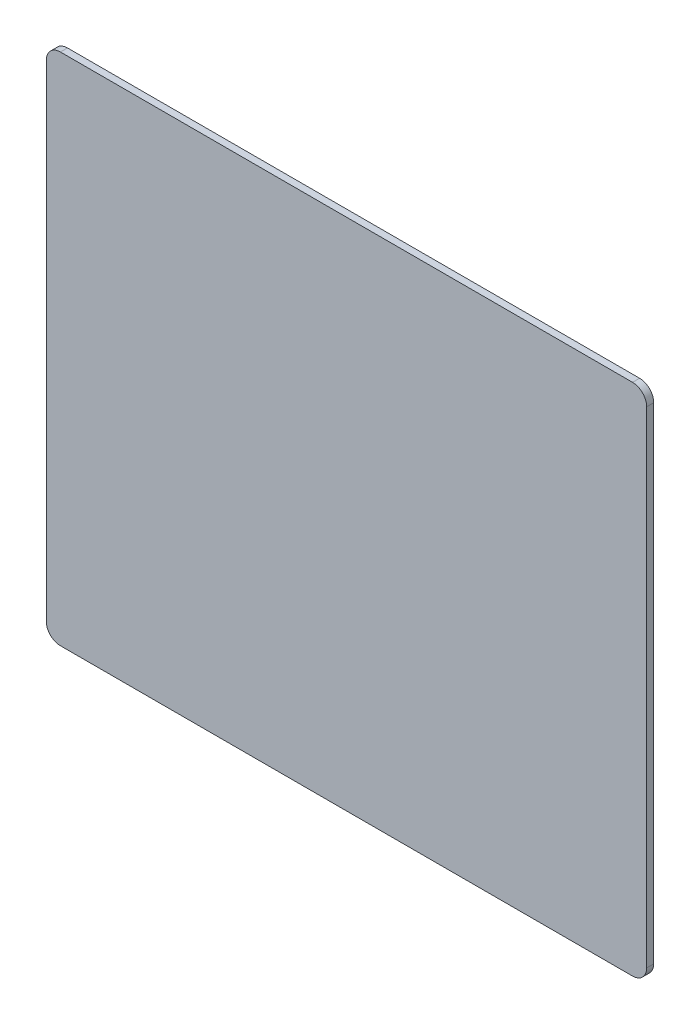
SolidWorks part; units mm, degrees
ref_plane "Plan de face" through (0, 0, 0) normal (0, 0, 1) x (1, 0, 0)
ref_plane "Plan de dessus" through (0, 0, 0) normal (0, 1, 0) x (1, 0, 0)
ref_plane "Plan de droite" through (0, 0, 0) normal (1, 0, 0) x (0, 0, -1)
sketch "Esquisse1" plane through (0, 0, 0) normal (0, 0, 1) x (1, 0, 0)
  line L1 (-40.5, 36.4) -> (40.5, 36.4)
  line L2 (-42.5, 34.4) -> (-42.5, -34.4)
  line L3 (-40.5, -36.4) -> (40.5, -36.4)
  line L4 (42.5, 34.4) -> (42.5, -34.4)
  line L5 (-42.5, 36.4) -> (42.5, -36.4) construction
  line L6 (-42.5, -36.4) -> (42.5, 36.4) construction
  arc A0 (-42.5, -34.4) -> (-40.5, -36.4) centre (-40.5, -34.4) ccw
  arc A1 (40.5, -36.4) -> (42.5, -34.4) centre (40.5, -34.4) ccw
  arc A2 (40.5, 36.4) -> (42.5, 34.4) centre (40.5, 34.4) cw
  arc A3 (-40.5, 36.4) -> (-42.5, 34.4) centre (-40.5, 34.4) ccw
  point P0 (0, 0)
  dimension "D3" = 2
  dimension "D1" = 85
  dimension "D2" = 72.8
extrude "Boss.-Extru.1" add sketch "Esquisse1" along normal blind 1
sketch "Esquisse2" plane through (0, 0, 0) normal (0, 0, -1) x (-1, 0, 0)
  line L0 (-35.5, 28.4) -> (-35.5, 19.4)
  line L1 (-35.5, 19.4) -> (-31.627, 18.4)
  line L2 (-31.627, 18.4) -> (-20.5, 18.4)
  line L3 (-20.5, 18.4) -> (-20.5, 28.4)
  line L4 (-20.5, 28.4) -> (-35.5, 28.4)
  line L5 (-42.5, -34.4) -> (-42.5, 34.4) construction
  line L6 (-40.5, 36.4) -> (40.5, 36.4) construction
  dimension "D1" = 15
  dimension "D2" = 10
  dimension "D3" = 9
  dimension "D4" = 4
  dimension "D5" = 7
  dimension "D6" = 8
extrude "Boss.-Extru.2" add sketch "Esquisse2" along normal blind 0.2
pattern_linear "Répétition linéaire1" count 4 spacing 19 along (-1, 0, 0) count 5 spacing 12 along (0, -1, 0) skipping (3, 3), (3, 4) of "Boss.-Extru.2"
sketch "Esquisse3" plane through (0, 0, 0) normal (0, 0, -1) x (-1, 0, 0)
  line L1 (21.5, -7.6) -> (36.5, -7.6) construction
  line L2 (36.5, -7.6) -> (36.5, -17.6) construction
  line L3 (36.5, -17.6) -> (21.5, -17.6) construction
  line L4 (21.5, -17.6) -> (21.5, -7.6) construction
  line L5 (36.5, -5.6) -> (36.5, 4.4) construction
  line L6 (21.5, 4.4) -> (21.5, -4.6) construction
  line L7 (6.373, -17.6) -> (17.5, -17.6) construction
  line L8 (17.5, -7.6) -> (2.5, -7.6) construction
  ellipse E0 centre (29, -12.6) end of major axis (36.5, -12.6) minor radius 5
extrude "Boss.-Extru.3" add sketch "Esquisse3" along normal blind 0.2
pattern_linear "Répétition linéaire2" count 2 spacing 12 along (0, -1, 0) of "Boss.-Extru.3"
sketch "Esquisse4" plane through (0, 0, -0.2) normal (0, 0, -1) x (-1, 0, 0)
  line L0 (-20.5, 18.4) -> (-20.5, 28.4) construction
  line L1 (-31.75, 20.4) -> (-20.5, 20.4) construction
  line L2 (-31.75, 20.4) -> (-31.75, 33.0905) construction
  line L4 (-20.5, 28.4) -> (-35.5, 28.4) construction
  line L5 (-12.75, 20.4) -> (-3.304, 20.4) construction
  line L6 (-1.5, 28.4) -> (-16.5, 28.4) construction
  line L7 (7, 20.4) -> (15.4189, 20.4) construction
  line L8 (27, 18.9) -> (33.7413, 18.9) construction
  line L9 (-30, 8.4) -> (-22.7278, 8.4) construction
  line L10 (-30, -3.6) -> (-22.7278, -3.6) construction
  line L11 (-11, 8.4) -> (-3.304, 8.4) construction
  line L12 (8, 8.4) -> (15.4189, 8.4) construction
  line L13 (24.3298, 8.4) -> (33.7413, 8.4) construction
  line L14 (24.3298, -3.6) -> (33.7413, -3.6) construction
  line L15 (8, -3.6) -> (14.3175, -3.6) construction
  line L16 (-11, -3.6) -> (-4.8059, -3.6) construction
  line L17 (-30, -15.6) -> (-22.7278, -15.6) construction
  line L18 (-11, -15.6) -> (-3.304, -15.6) construction
  line L19 (8, -15.6) -> (14.3175, -15.6) construction
  line L20 (-31.75, -27.6) -> (-23.9293, -27.6) construction
  line L21 (23.5, -15.6) -> (35.7582, -15.6) construction
  line L22 (-11, -27.6) -> (-4.8059, -27.6) construction
  line L23 (6, -27.6) -> (14.3175, -27.6) construction
  line L24 (23.5, -26.6827) -> (31.8102, -26.6827) construction
  line L25 (17.5, 28.4) -> (2.5, 28.4) construction
  line L26 (36.5, 28.4) -> (21.5, 28.4) construction
  line L27 (36.5, 28.4) -> (21.5, 28.4) construction
  line L28 (-20.5, 16.4) -> (-35.5, 16.4) construction
  line L29 (-20.5, 4.4) -> (-35.5, 4.4) construction
  line L30 (-20.5, -7.6) -> (-35.5, -7.6) construction
  line L31 (-20.5, -19.6) -> (-35.5, -19.6) construction
  line L32 (-1.5, 16.4) -> (-16.5, 16.4) construction
  line L33 (17.5, 16.4) -> (2.5, 16.4) construction
  line L34 (28, 8.4) -> (28, 12.4)
  line L35 (28, 12.4) -> (26.5, 12.4)
  line L36 (26.5, 12.4) -> (29, 15.4)
  line L37 (29, 15.4) -> (31.5, 12.4)
  line L38 (31.5, 12.4) -> (30, 12.4)
  line L39 (30, 12.4) -> (30, 8.4)
  line L40 (30, 8.4) -> (28, 8.4)
  line L41 (36.5, 16.4) -> (21.5, 16.4) construction
  line L44 (28, 3.4) -> (28, -0.6)
  line L52 (28, -0.6) -> (26.5, -0.6)
  line L53 (26.5, -0.6) -> (29, -3.6)
  line L54 (29, -3.6) -> (31.5, -0.6)
  line L55 (31.5, -0.6) -> (30, -0.6)
  line L56 (30, -0.6) -> (30, 3.4)
  line L57 (30, 3.4) -> (28, 3.4)
  line L58 (-24, -23.6) -> (-24, -25.6)
  line L59 (-24, -25.6) -> (-28, -25.6)
  line L60 (-28, -25.6) -> (-28, -27.1)
  line L61 (-28, -27.1) -> (-31, -24.6)
  line L62 (-31, -24.6) -> (-28, -22.1)
  line L63 (-28, -22.1) -> (-28, -23.6)
  line L64 (-28, -23.6) -> (-24, -23.6)
  line L65 (6, -23.6) -> (6, -25.6)
  line L66 (6, -25.6) -> (10, -25.6)
  line L67 (10, -25.6) -> (10, -27.1)
  line L68 (10, -27.1) -> (13, -24.6)
  line L69 (13, -24.6) -> (10, -22.1)
  line L70 (10, -22.1) -> (10, -23.6)
  line L71 (10, -23.6) -> (6, -23.6)
  line L72 (-20.5, -19.6) -> (-35.5, -19.6) construction
  line L73 (-20.5, -29.6) -> (-20.5, -19.6) construction
  line L74 (17.5, -19.6) -> (2.5, -19.6) construction
  line L75 (36.5, 4.4) -> (21.5, 4.4) construction
  text T0 "F1" font "Century Gothic" height in points 22
  text T1 "F2" font "Century Gothic" height in points 22
  text T2 "#" font "Century Gothic" height in points 22
  text T3 "*" font "Century Gothic" height in points 22
  text T4 "1" font "Century Gothic" height in points 22
  text T5 "2" font "Century Gothic" height in points 22
  text T6 "3" font "Century Gothic" height in points 22
  text T7 "4" font "Century Gothic" height in points 22
  text T8 "5" font "Century Gothic" height in points 22
  text T9 "6" font "Century Gothic" height in points 22
  text T10 "7" font "Century Gothic" height in points 22
  text T11 "8" font "Century Gothic" height in points 22
  text T12 "9" font "Century Gothic" height in points 22
  text T13 "0" font "Century Gothic" height in points 22
  text T14 "Esc" font "Century Gothic" height in points 20
  text T15 "Ent" font "Century Gothic" height in points 20
  point P10 (-28, 28.4)
  point P14 (-9, 28.4)
  point P54 (10, 28.4)
  point P58 (29, 28.4)
  point P72 (-28, 16.4)
  point P75 (-9, 16.4)
  point P78 (10, 16.4)
  point P87 (29, 16.4)
  point P113 (-28, -19.6)
  point P116 (-20.5, -24.6)
  point P117 (-24, -24.6)
  point P123 (10, -19.6)
  point P126 (29, 4.4)
  dimension "D1" = 3.75
  dimension "D2" = 8
  dimension "D3" = 3.75
  dimension "D4" = 3
  dimension "D5" = 2
  dimension "D6" = 9.5
  dimension "D7" = 8
  dimension "D8" = 8
  dimension "D9" = 8
  dimension "D10" = 8
  dimension "D11" = 2
  dimension "D12" = 2
  dimension "D13" = 2
  dimension "D14" = 7
  dimension "D15" = 2
  dimension "D16" = 1
  dimension "D17" = 4
  dimension "D18" = 5
  dimension "D19" = 2.5
  dimension "D20" = 4
  dimension "D21" = 7
  dimension "D22" = 2
  dimension "D23" = 1
  dimension "D24" = 2
  dimension "D25" = 7
  dimension "D26" = 7
  dimension "D27" = 4
  dimension "D28" = 5
  dimension "D29" = 1
  dimension "D30" = 2.5
  dimension "D31" = 4
  dimension "D32" = 2.5
  dimension "D33" = 5.5
extrude "Boss.-Extru.4" add sketch "Esquisse4" along normal blind 0.2
